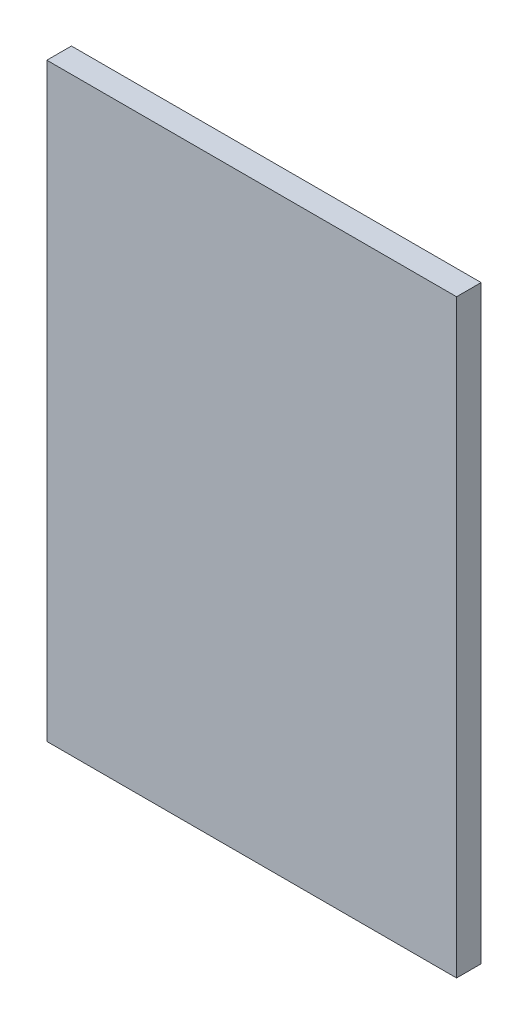
SolidWorks part; units mm, degrees
ref_plane "前视基准面" through (0, 0, 0) normal (0, 0, 1) x (1, 0, 0)
ref_plane "上视基准面" through (0, 0, 0) normal (0, 1, 0) x (1, 0, 0)
ref_plane "右视基准面" through (0, 0, 0) normal (1, 0, 0) x (0, 0, -1)
sketch "草图1" plane through (0, 0, 0) normal (0, 0, 1) x (1, 0, 0)
  line L1 (-6.3516, 7.5203) -> (43.6484, 7.5203)
  line L2 (-6.3516, 7.5203) -> (-6.3516, -64.4797)
  line L3 (-6.3516, -64.4797) -> (43.6484, -64.4797)
  line L4 (43.6484, 7.5203) -> (43.6484, -64.4797)
  dimension "D1" = 50
  dimension "D2" = 72
extrude "凸台-拉伸1" add sketch "草图1" along normal blind 3
